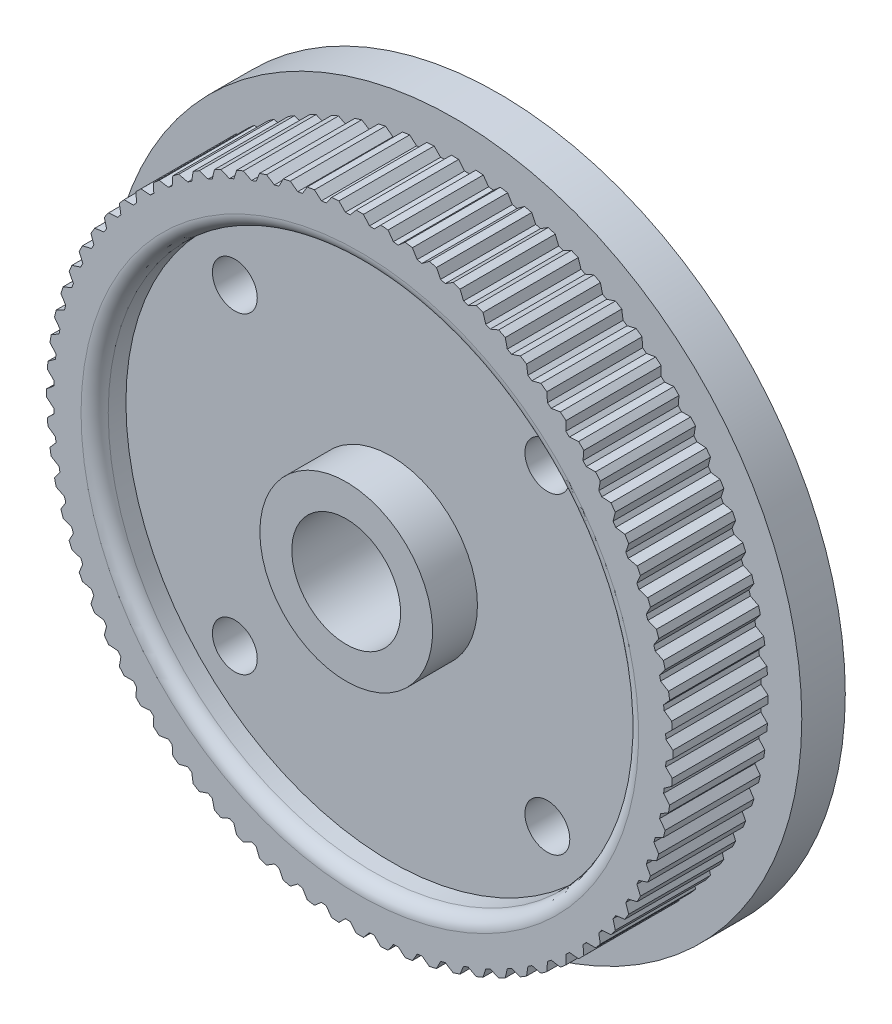
SolidWorks part; units mm, degrees
ref_plane "Front Plane" through (0, 0, 0) normal (0, 0, 1) x (1, 0, 0)
ref_plane "Top Plane" through (0, 0, 0) normal (0, 1, 0) x (1, 0, 0)
ref_plane "Right Plane" through (0, 0, 0) normal (1, 0, 0) x (0, 0, -1)
sketch "Sketch1" plane through (0, 0, 0) normal (1, 0, 0) x (0, 0, -1)
  line L0 (0, 4) -> (0, 8.5)
  line L1 (0, 8.5) -> (1, 8.5)
  line L2 (1, 8.5) -> (1, 23.025)
  line L3 (1, 23.025) -> (8, 23.025)
  line L4 (8, 25.5) -> (8, 23.025)
  line L5 (8, 25.5) -> (11.2, 25.5)
  line L6 (11.2, 25.5) -> (11.2, 8.5)
  line L7 (11.2, 8.5) -> (17.5, 8.5)
  line L8 (17.5, 8.5) -> (17.5, 4)
  line L9 (17.5, 4) -> (0, 4)
  line L10 (0, 0) -> (36.0343, 0) construction
  dimension "D1" = 8
  dimension "D2" = 17
  dimension "D3" = 17.5
  dimension "D4" = 51
  dimension "D5" = 46.05
  dimension "D6" = 8
  dimension "D7" = 1
  dimension "D8" = 11.2
revolve "Revolve1" add sketch "Sketch1" angle 360 about L10
sketch "Sketch2" plane through (0, 0, -1) normal (0, 0, 1) x (1, 0, 0)
  line L0 (0, 23.025) -> (0, 0) construction
  line L1 (0, 0) -> (1.8065, 22.954) construction
  line L2 (0.27, 23.0234) -> (0.7059, 22.5039)
  line L3 (1.0619, 22.4899) -> (1.5372, 22.9736)
  line L4 (2.8232, 22.3373) -> (3.335, 22.7822)
  line L5 (2.0756, 22.9313) -> (2.4694, 22.3792)
  line L6 (4.567, 22.0469) -> (5.1122, 22.4503)
  line L7 (3.8683, 22.6977) -> (4.2176, 22.1164)
  line L8 (6.2827, 21.6206) -> (6.8578, 21.98)
  line L9 (5.6372, 22.3242) -> (5.9398, 21.7174)
  line L10 (7.9597, 21.0611) -> (8.5612, 21.3742)
  line L11 (7.3714, 21.8131) -> (7.6254, 21.1844)
  line L12 (9.5876, 20.3716) -> (10.2118, 20.6366)
  line L13 (9.0601, 21.1675) -> (9.264, 20.5208)
  line L14 (11.1564, 19.5566) -> (11.7995, 19.7718)
  line L15 (10.693, 20.3914) -> (10.8455, 19.7307)
  line L16 (12.6564, 18.621) -> (13.3144, 18.785)
  line L17 (12.2599, 19.4896) -> (12.3602, 18.8189)
  line L18 (14.0784, 17.5706) -> (14.7472, 17.6825)
  line L19 (13.7513, 18.4676) -> (13.7986, 17.7911)
  line L20 (15.4135, 16.4118) -> (16.0891, 16.4709)
  line L21 (15.1578, 17.3318) -> (15.1519, 16.6537)
  line L22 (16.6537, 15.1519) -> (17.3318, 15.1578)
  line L23 (16.4709, 16.0891) -> (16.4118, 15.4135)
  line L24 (17.7911, 13.7986) -> (18.4676, 13.7513)
  line L25 (17.6825, 14.7472) -> (17.5706, 14.0784)
  line L26 (18.8189, 12.3602) -> (19.4896, 12.2599)
  line L27 (18.785, 13.3144) -> (18.621, 12.6564)
  line L28 (19.7307, 10.8455) -> (20.3914, 10.693)
  line L29 (19.7718, 11.7995) -> (19.5566, 11.1564)
  line L30 (20.5208, 9.264) -> (21.1675, 9.0601)
  line L31 (20.6366, 10.2118) -> (20.3716, 9.5876)
  line L32 (21.1844, 7.6254) -> (21.8131, 7.3714)
  line L33 (21.3742, 8.5612) -> (21.0611, 7.9597)
  line L34 (21.7174, 5.9398) -> (22.3242, 5.6372)
  line L35 (21.98, 6.8578) -> (21.6206, 6.2827)
  line L36 (22.1164, 4.2176) -> (22.6977, 3.8683)
  line L37 (22.4503, 5.1122) -> (22.0469, 4.567)
  line L38 (22.3792, 2.4694) -> (22.9313, 2.0756)
  line L39 (22.7822, 3.335) -> (22.3373, 2.8232)
  line L40 (22.5039, 0.7059) -> (23.0234, 0.27)
  line L41 (22.9736, 1.5372) -> (22.4899, 1.0619)
  line L42 (22.4899, -1.0619) -> (22.9736, -1.5372)
  line L43 (23.0234, -0.27) -> (22.5039, -0.7059)
  line L44 (22.3373, -2.8232) -> (22.7822, -3.335)
  line L45 (22.9313, -2.0756) -> (22.3792, -2.4694)
  line L46 (22.0469, -4.567) -> (22.4503, -5.1122)
  line L47 (22.6977, -3.8683) -> (22.1164, -4.2176)
  line L48 (21.6206, -6.2827) -> (21.98, -6.8578)
  line L49 (22.3242, -5.6372) -> (21.7174, -5.9398)
  line L50 (21.0611, -7.9597) -> (21.3742, -8.5612)
  line L51 (21.8131, -7.3714) -> (21.1844, -7.6254)
  line L52 (20.3716, -9.5876) -> (20.6366, -10.2118)
  line L53 (21.1675, -9.0601) -> (20.5208, -9.264)
  line L54 (19.5566, -11.1564) -> (19.7718, -11.7995)
  line L55 (20.3914, -10.693) -> (19.7307, -10.8455)
  line L56 (18.621, -12.6564) -> (18.785, -13.3144)
  line L57 (19.4896, -12.2599) -> (18.8189, -12.3602)
  line L58 (17.5706, -14.0784) -> (17.6825, -14.7472)
  line L59 (18.4676, -13.7513) -> (17.7911, -13.7986)
  line L60 (16.4118, -15.4135) -> (16.4709, -16.0891)
  line L61 (17.3318, -15.1578) -> (16.6537, -15.1519)
  line L62 (15.1519, -16.6537) -> (15.1578, -17.3318)
  line L63 (16.0891, -16.4709) -> (15.4135, -16.4118)
  line L64 (13.7986, -17.7911) -> (13.7513, -18.4676)
  line L65 (14.7472, -17.6825) -> (14.0784, -17.5706)
  line L66 (12.3602, -18.8189) -> (12.2599, -19.4896)
  line L67 (13.3144, -18.785) -> (12.6564, -18.621)
  line L68 (10.8455, -19.7307) -> (10.693, -20.3914)
  line L69 (11.7995, -19.7718) -> (11.1564, -19.5566)
  line L70 (9.264, -20.5208) -> (9.0601, -21.1675)
  line L71 (10.2118, -20.6366) -> (9.5876, -20.3716)
  line L72 (7.6254, -21.1844) -> (7.3714, -21.8131)
  line L73 (8.5612, -21.3742) -> (7.9597, -21.0611)
  line L74 (5.9398, -21.7174) -> (5.6372, -22.3242)
  line L75 (6.8578, -21.98) -> (6.2827, -21.6206)
  line L76 (4.2176, -22.1164) -> (3.8683, -22.6977)
  line L77 (5.1122, -22.4503) -> (4.567, -22.0469)
  line L78 (2.4694, -22.3792) -> (2.0756, -22.9313)
  line L79 (3.335, -22.7822) -> (2.8232, -22.3373)
  line L80 (0.7059, -22.5039) -> (0.27, -23.0234)
  line L81 (1.5372, -22.9736) -> (1.0619, -22.4899)
  line L82 (-1.0619, -22.4899) -> (-1.5372, -22.9736)
  line L83 (-0.27, -23.0234) -> (-0.7059, -22.5039)
  line L84 (-2.8232, -22.3373) -> (-3.335, -22.7822)
  line L85 (-2.0756, -22.9313) -> (-2.4694, -22.3792)
  line L86 (-4.567, -22.0469) -> (-5.1122, -22.4503)
  line L87 (-3.8683, -22.6977) -> (-4.2176, -22.1164)
  line L88 (-6.2827, -21.6206) -> (-6.8578, -21.98)
  line L89 (-5.6372, -22.3242) -> (-5.9398, -21.7174)
  line L90 (-7.9597, -21.0611) -> (-8.5612, -21.3742)
  line L91 (-7.3714, -21.8131) -> (-7.6254, -21.1844)
  line L92 (-9.5876, -20.3716) -> (-10.2118, -20.6366)
  line L93 (-9.0601, -21.1675) -> (-9.264, -20.5208)
  line L94 (-11.1564, -19.5566) -> (-11.7995, -19.7718)
  line L95 (-10.693, -20.3914) -> (-10.8455, -19.7307)
  line L96 (-12.6564, -18.621) -> (-13.3144, -18.785)
  line L97 (-12.2599, -19.4896) -> (-12.3602, -18.8189)
  line L98 (-14.0784, -17.5706) -> (-14.7472, -17.6825)
  line L99 (-13.7513, -18.4676) -> (-13.7986, -17.7911)
  line L100 (-15.4135, -16.4118) -> (-16.0891, -16.4709)
  line L101 (-15.1578, -17.3318) -> (-15.1519, -16.6537)
  line L102 (-16.6537, -15.1519) -> (-17.3318, -15.1578)
  line L103 (-16.4709, -16.0891) -> (-16.4118, -15.4135)
  line L104 (-17.7911, -13.7986) -> (-18.4676, -13.7513)
  line L105 (-17.6825, -14.7472) -> (-17.5706, -14.0784)
  line L106 (-18.8189, -12.3602) -> (-19.4896, -12.2599)
  line L107 (-18.785, -13.3144) -> (-18.621, -12.6564)
  line L108 (-19.7307, -10.8455) -> (-20.3914, -10.693)
  line L109 (-19.7718, -11.7995) -> (-19.5566, -11.1564)
  line L110 (-20.5208, -9.264) -> (-21.1675, -9.0601)
  line L111 (-20.6366, -10.2118) -> (-20.3716, -9.5876)
  line L112 (-21.1844, -7.6254) -> (-21.8131, -7.3714)
  line L113 (-21.3742, -8.5612) -> (-21.0611, -7.9597)
  line L114 (-21.7174, -5.9398) -> (-22.3242, -5.6372)
  line L115 (-21.98, -6.8578) -> (-21.6206, -6.2827)
  line L116 (-22.1164, -4.2176) -> (-22.6977, -3.8683)
  line L117 (-22.4503, -5.1122) -> (-22.0469, -4.567)
  line L118 (-22.3792, -2.4694) -> (-22.9313, -2.0756)
  line L119 (-22.7822, -3.335) -> (-22.3373, -2.8232)
  line L120 (-22.5039, -0.7059) -> (-23.0234, -0.27)
  line L121 (-22.9736, -1.5372) -> (-22.4899, -1.0619)
  line L122 (-22.4899, 1.0619) -> (-22.9736, 1.5372)
  line L123 (-23.0234, 0.27) -> (-22.5039, 0.7059)
  line L124 (-22.3373, 2.8232) -> (-22.7822, 3.335)
  line L125 (-22.9313, 2.0756) -> (-22.3792, 2.4694)
  line L126 (-22.0469, 4.567) -> (-22.4503, 5.1122)
  line L127 (-22.6977, 3.8683) -> (-22.1164, 4.2176)
  line L128 (-21.6206, 6.2827) -> (-21.98, 6.8578)
  line L129 (-22.3242, 5.6372) -> (-21.7174, 5.9398)
  line L130 (-21.0611, 7.9597) -> (-21.3742, 8.5612)
  line L131 (-21.8131, 7.3714) -> (-21.1844, 7.6254)
  line L132 (-20.3716, 9.5876) -> (-20.6366, 10.2118)
  line L133 (-21.1675, 9.0601) -> (-20.5208, 9.264)
  line L134 (-19.5566, 11.1564) -> (-19.7718, 11.7995)
  line L135 (-20.3914, 10.693) -> (-19.7307, 10.8455)
  line L136 (-18.621, 12.6564) -> (-18.785, 13.3144)
  line L137 (-19.4896, 12.2599) -> (-18.8189, 12.3602)
  line L138 (-17.5706, 14.0784) -> (-17.6825, 14.7472)
  line L139 (-18.4676, 13.7513) -> (-17.7911, 13.7986)
  line L140 (-16.4118, 15.4135) -> (-16.4709, 16.0891)
  line L141 (-17.3318, 15.1578) -> (-16.6537, 15.1519)
  line L142 (-15.1519, 16.6537) -> (-15.1578, 17.3318)
  line L143 (-16.0891, 16.4709) -> (-15.4135, 16.4118)
  line L144 (-13.7986, 17.7911) -> (-13.7513, 18.4676)
  line L145 (-14.7472, 17.6825) -> (-14.0784, 17.5706)
  line L146 (-12.3602, 18.8189) -> (-12.2599, 19.4896)
  line L147 (-13.3144, 18.785) -> (-12.6564, 18.621)
  line L148 (-10.8455, 19.7307) -> (-10.693, 20.3914)
  line L149 (-11.7995, 19.7718) -> (-11.1564, 19.5566)
  line L150 (-9.264, 20.5208) -> (-9.0601, 21.1675)
  line L151 (-10.2118, 20.6366) -> (-9.5876, 20.3716)
  line L152 (-7.6254, 21.1844) -> (-7.3714, 21.8131)
  line L153 (-8.5612, 21.3742) -> (-7.9597, 21.0611)
  line L154 (-5.9398, 21.7174) -> (-5.6372, 22.3242)
  line L155 (-6.8578, 21.98) -> (-6.2827, 21.6206)
  line L156 (-4.2176, 22.1164) -> (-3.8683, 22.6977)
  line L157 (-5.1122, 22.4503) -> (-4.567, 22.0469)
  line L158 (-2.4694, 22.3792) -> (-2.0756, 22.9313)
  line L159 (-3.335, 22.7822) -> (-2.8232, 22.3373)
  line L160 (-0.7059, 22.5039) -> (-0.27, 23.0234)
  line L161 (-1.5372, 22.9736) -> (-1.0619, 22.4899)
  circle A0 centre (0, 0) radius 23.025 construction
  circle A1 centre (0, 0) radius 23.025 construction
  arc A2 (0.7059, 22.5039) -> (1.0619, 22.4899) centre (0, 0) cw
  arc A3 (0.27, 23.0234) -> (0, 23.025) centre (0, 0) ccw
  arc A4 (1.5372, 22.9736) -> (1.8065, 22.954) centre (0, 0) cw
  arc A5 (3.335, 22.7822) -> (3.6019, 22.7415) centre (0, 0) cw
  arc A6 (2.4694, 22.3792) -> (2.8232, 22.3373) centre (0, 0) cw
  arc A7 (2.0756, 22.9313) -> (1.8065, 22.954) centre (0, 0) ccw
  arc A8 (5.1122, 22.4503) -> (5.3751, 22.3888) centre (0, 0) cw
  arc A9 (4.2176, 22.1164) -> (4.567, 22.0469) centre (0, 0) cw
  arc A10 (3.8683, 22.6977) -> (3.6019, 22.7415) centre (0, 0) ccw
  arc A11 (6.8578, 21.98) -> (7.1151, 21.8981) centre (0, 0) cw
  arc A12 (5.9398, 21.7174) -> (6.2827, 21.6206) centre (0, 0) cw
  arc A13 (5.6372, 22.3242) -> (5.3751, 22.3888) centre (0, 0) ccw
  arc A14 (8.5612, 21.3742) -> (8.8113, 21.2723) centre (0, 0) cw
  arc A15 (7.6254, 21.1844) -> (7.9597, 21.0611) centre (0, 0) cw
  arc A16 (7.3714, 21.8131) -> (7.1151, 21.8981) centre (0, 0) ccw
  arc A17 (10.2118, 20.6366) -> (10.4531, 20.5154) centre (0, 0) cw
  arc A18 (9.264, 20.5208) -> (9.5876, 20.3716) centre (0, 0) cw
  arc A19 (9.0601, 21.1675) -> (8.8113, 21.2723) centre (0, 0) ccw
  arc A20 (11.7995, 19.7718) -> (12.0305, 19.632) centre (0, 0) cw
  arc A21 (10.8455, 19.7307) -> (11.1564, 19.5566) centre (0, 0) cw
  arc A22 (10.693, 20.3914) -> (10.4531, 20.5154) centre (0, 0) ccw
  arc A23 (13.3144, 18.785) -> (13.5338, 18.6276) centre (0, 0) cw
  arc A24 (12.3602, 18.8189) -> (12.6564, 18.621) centre (0, 0) cw
  arc A25 (12.2599, 19.4896) -> (12.0305, 19.632) centre (0, 0) ccw
  arc A26 (14.7472, 17.6825) -> (14.9535, 17.5083) centre (0, 0) cw
  arc A27 (13.7986, 17.7911) -> (14.0784, 17.5706) centre (0, 0) cw
  arc A28 (13.7513, 18.4676) -> (13.5338, 18.6276) centre (0, 0) ccw
  arc A29 (16.0891, 16.4709) -> (16.2811, 16.2811) centre (0, 0) cw
  arc A30 (15.1519, 16.6537) -> (15.4135, 16.4118) centre (0, 0) cw
  arc A31 (15.1578, 17.3318) -> (14.9535, 17.5083) centre (0, 0) ccw
  arc A32 (17.3318, 15.1578) -> (17.5083, 14.9535) centre (0, 0) cw
  arc A33 (16.4118, 15.4135) -> (16.6537, 15.1519) centre (0, 0) cw
  arc A34 (16.4709, 16.0891) -> (16.2811, 16.2811) centre (0, 0) ccw
  arc A35 (18.4676, 13.7513) -> (18.6276, 13.5338) centre (0, 0) cw
  arc A36 (17.5706, 14.0784) -> (17.7911, 13.7986) centre (0, 0) cw
  arc A37 (17.6825, 14.7472) -> (17.5083, 14.9535) centre (0, 0) ccw
  arc A38 (19.4896, 12.2599) -> (19.632, 12.0305) centre (0, 0) cw
  arc A39 (18.621, 12.6564) -> (18.8189, 12.3602) centre (0, 0) cw
  arc A40 (18.785, 13.3144) -> (18.6276, 13.5338) centre (0, 0) ccw
  arc A41 (20.3914, 10.693) -> (20.5154, 10.4531) centre (0, 0) cw
  arc A42 (19.5566, 11.1564) -> (19.7307, 10.8455) centre (0, 0) cw
  arc A43 (19.7718, 11.7995) -> (19.632, 12.0305) centre (0, 0) ccw
  arc A44 (21.1675, 9.0601) -> (21.2723, 8.8113) centre (0, 0) cw
  arc A45 (20.3716, 9.5876) -> (20.5208, 9.264) centre (0, 0) cw
  arc A46 (20.6366, 10.2118) -> (20.5154, 10.4531) centre (0, 0) ccw
  arc A47 (21.8131, 7.3714) -> (21.8981, 7.1151) centre (0, 0) cw
  arc A48 (21.0611, 7.9597) -> (21.1844, 7.6254) centre (0, 0) cw
  arc A49 (21.3742, 8.5612) -> (21.2723, 8.8113) centre (0, 0) ccw
  arc A50 (22.3242, 5.6372) -> (22.3888, 5.3751) centre (0, 0) cw
  arc A51 (21.6206, 6.2827) -> (21.7174, 5.9398) centre (0, 0) cw
  arc A52 (21.98, 6.8578) -> (21.8981, 7.1151) centre (0, 0) ccw
  arc A53 (22.6977, 3.8683) -> (22.7415, 3.6019) centre (0, 0) cw
  arc A54 (22.0469, 4.567) -> (22.1164, 4.2176) centre (0, 0) cw
  arc A55 (22.4503, 5.1122) -> (22.3888, 5.3751) centre (0, 0) ccw
  arc A56 (22.9313, 2.0756) -> (22.954, 1.8065) centre (0, 0) cw
  arc A57 (22.3373, 2.8232) -> (22.3792, 2.4694) centre (0, 0) cw
  arc A58 (22.7822, 3.335) -> (22.7415, 3.6019) centre (0, 0) ccw
  arc A59 (23.0234, 0.27) -> (23.025, 0) centre (0, 0) cw
  arc A60 (22.4899, 1.0619) -> (22.5039, 0.7059) centre (0, 0) cw
  arc A61 (22.9736, 1.5372) -> (22.954, 1.8065) centre (0, 0) ccw
  arc A62 (22.9736, -1.5372) -> (22.954, -1.8065) centre (0, 0) cw
  arc A63 (22.5039, -0.7059) -> (22.4899, -1.0619) centre (0, 0) cw
  arc A64 (23.0234, -0.27) -> (23.025, 0) centre (0, 0) ccw
  arc A65 (22.7822, -3.335) -> (22.7415, -3.6019) centre (0, 0) cw
  arc A66 (22.3792, -2.4694) -> (22.3373, -2.8232) centre (0, 0) cw
  arc A67 (22.9313, -2.0756) -> (22.954, -1.8065) centre (0, 0) ccw
  arc A68 (22.4503, -5.1122) -> (22.3888, -5.3751) centre (0, 0) cw
  arc A69 (22.1164, -4.2176) -> (22.0469, -4.567) centre (0, 0) cw
  arc A70 (22.6977, -3.8683) -> (22.7415, -3.6019) centre (0, 0) ccw
  arc A71 (21.98, -6.8578) -> (21.8981, -7.1151) centre (0, 0) cw
  arc A72 (21.7174, -5.9398) -> (21.6206, -6.2827) centre (0, 0) cw
  arc A73 (22.3242, -5.6372) -> (22.3888, -5.3751) centre (0, 0) ccw
  arc A74 (21.3742, -8.5612) -> (21.2723, -8.8113) centre (0, 0) cw
  arc A75 (21.1844, -7.6254) -> (21.0611, -7.9597) centre (0, 0) cw
  arc A76 (21.8131, -7.3714) -> (21.8981, -7.1151) centre (0, 0) ccw
  arc A77 (20.6366, -10.2118) -> (20.5154, -10.4531) centre (0, 0) cw
  arc A78 (20.5208, -9.264) -> (20.3716, -9.5876) centre (0, 0) cw
  arc A79 (21.1675, -9.0601) -> (21.2723, -8.8113) centre (0, 0) ccw
  arc A80 (19.7718, -11.7995) -> (19.632, -12.0305) centre (0, 0) cw
  arc A81 (19.7307, -10.8455) -> (19.5566, -11.1564) centre (0, 0) cw
  arc A82 (20.3914, -10.693) -> (20.5154, -10.4531) centre (0, 0) ccw
  arc A83 (18.785, -13.3144) -> (18.6276, -13.5338) centre (0, 0) cw
  arc A84 (18.8189, -12.3602) -> (18.621, -12.6564) centre (0, 0) cw
  arc A85 (19.4896, -12.2599) -> (19.632, -12.0305) centre (0, 0) ccw
  arc A86 (17.6825, -14.7472) -> (17.5083, -14.9535) centre (0, 0) cw
  arc A87 (17.7911, -13.7986) -> (17.5706, -14.0784) centre (0, 0) cw
  arc A88 (18.4676, -13.7513) -> (18.6276, -13.5338) centre (0, 0) ccw
  arc A89 (16.4709, -16.0891) -> (16.2811, -16.2811) centre (0, 0) cw
  arc A90 (16.6537, -15.1519) -> (16.4118, -15.4135) centre (0, 0) cw
  arc A91 (17.3318, -15.1578) -> (17.5083, -14.9535) centre (0, 0) ccw
  arc A92 (15.1578, -17.3318) -> (14.9535, -17.5083) centre (0, 0) cw
  arc A93 (15.4135, -16.4118) -> (15.1519, -16.6537) centre (0, 0) cw
  arc A94 (16.0891, -16.4709) -> (16.2811, -16.2811) centre (0, 0) ccw
  arc A95 (13.7513, -18.4676) -> (13.5338, -18.6276) centre (0, 0) cw
  arc A96 (14.0784, -17.5706) -> (13.7986, -17.7911) centre (0, 0) cw
  arc A97 (14.7472, -17.6825) -> (14.9535, -17.5083) centre (0, 0) ccw
  arc A98 (12.2599, -19.4896) -> (12.0305, -19.632) centre (0, 0) cw
  arc A99 (12.6564, -18.621) -> (12.3602, -18.8189) centre (0, 0) cw
  arc A100 (13.3144, -18.785) -> (13.5338, -18.6276) centre (0, 0) ccw
  arc A101 (10.693, -20.3914) -> (10.4531, -20.5154) centre (0, 0) cw
  arc A102 (11.1564, -19.5566) -> (10.8455, -19.7307) centre (0, 0) cw
  arc A103 (11.7995, -19.7718) -> (12.0305, -19.632) centre (0, 0) ccw
  arc A104 (9.0601, -21.1675) -> (8.8113, -21.2723) centre (0, 0) cw
  arc A105 (9.5876, -20.3716) -> (9.264, -20.5208) centre (0, 0) cw
  arc A106 (10.2118, -20.6366) -> (10.4531, -20.5154) centre (0, 0) ccw
  arc A107 (7.3714, -21.8131) -> (7.1151, -21.8981) centre (0, 0) cw
  arc A108 (7.9597, -21.0611) -> (7.6254, -21.1844) centre (0, 0) cw
  arc A109 (8.5612, -21.3742) -> (8.8113, -21.2723) centre (0, 0) ccw
  arc A110 (5.6372, -22.3242) -> (5.3751, -22.3888) centre (0, 0) cw
  arc A111 (6.2827, -21.6206) -> (5.9398, -21.7174) centre (0, 0) cw
  arc A112 (6.8578, -21.98) -> (7.1151, -21.8981) centre (0, 0) ccw
  arc A113 (3.8683, -22.6977) -> (3.6019, -22.7415) centre (0, 0) cw
  arc A114 (4.567, -22.0469) -> (4.2176, -22.1164) centre (0, 0) cw
  arc A115 (5.1122, -22.4503) -> (5.3751, -22.3888) centre (0, 0) ccw
  arc A116 (2.0756, -22.9313) -> (1.8065, -22.954) centre (0, 0) cw
  arc A117 (2.8232, -22.3373) -> (2.4694, -22.3792) centre (0, 0) cw
  arc A118 (3.335, -22.7822) -> (3.6019, -22.7415) centre (0, 0) ccw
  arc A119 (0.27, -23.0234) -> (0, -23.025) centre (0, 0) cw
  arc A120 (1.0619, -22.4899) -> (0.7059, -22.5039) centre (0, 0) cw
  arc A121 (1.5372, -22.9736) -> (1.8065, -22.954) centre (0, 0) ccw
  arc A122 (-1.5372, -22.9736) -> (-1.8065, -22.954) centre (0, 0) cw
  arc A123 (-0.7059, -22.5039) -> (-1.0619, -22.4899) centre (0, 0) cw
  arc A124 (-0.27, -23.0234) -> (0, -23.025) centre (0, 0) ccw
  arc A125 (-3.335, -22.7822) -> (-3.6019, -22.7415) centre (0, 0) cw
  arc A126 (-2.4694, -22.3792) -> (-2.8232, -22.3373) centre (0, 0) cw
  arc A127 (-2.0756, -22.9313) -> (-1.8065, -22.954) centre (0, 0) ccw
  arc A128 (-5.1122, -22.4503) -> (-5.3751, -22.3888) centre (0, 0) cw
  arc A129 (-4.2176, -22.1164) -> (-4.567, -22.0469) centre (0, 0) cw
  arc A130 (-3.8683, -22.6977) -> (-3.6019, -22.7415) centre (0, 0) ccw
  arc A131 (-6.8578, -21.98) -> (-7.1151, -21.8981) centre (0, 0) cw
  arc A132 (-5.9398, -21.7174) -> (-6.2827, -21.6206) centre (0, 0) cw
  arc A133 (-5.6372, -22.3242) -> (-5.3751, -22.3888) centre (0, 0) ccw
  arc A134 (-8.5612, -21.3742) -> (-8.8113, -21.2723) centre (0, 0) cw
  arc A135 (-7.6254, -21.1844) -> (-7.9597, -21.0611) centre (0, 0) cw
  arc A136 (-7.3714, -21.8131) -> (-7.1151, -21.8981) centre (0, 0) ccw
  arc A137 (-10.2118, -20.6366) -> (-10.4531, -20.5154) centre (0, 0) cw
  arc A138 (-9.264, -20.5208) -> (-9.5876, -20.3716) centre (0, 0) cw
  arc A139 (-9.0601, -21.1675) -> (-8.8113, -21.2723) centre (0, 0) ccw
  arc A140 (-11.7995, -19.7718) -> (-12.0305, -19.632) centre (0, 0) cw
  arc A141 (-10.8455, -19.7307) -> (-11.1564, -19.5566) centre (0, 0) cw
  arc A142 (-10.693, -20.3914) -> (-10.4531, -20.5154) centre (0, 0) ccw
  arc A143 (-13.3144, -18.785) -> (-13.5338, -18.6276) centre (0, 0) cw
  arc A144 (-12.3602, -18.8189) -> (-12.6564, -18.621) centre (0, 0) cw
  arc A145 (-12.2599, -19.4896) -> (-12.0305, -19.632) centre (0, 0) ccw
  arc A146 (-14.7472, -17.6825) -> (-14.9535, -17.5083) centre (0, 0) cw
  arc A147 (-13.7986, -17.7911) -> (-14.0784, -17.5706) centre (0, 0) cw
  arc A148 (-13.7513, -18.4676) -> (-13.5338, -18.6276) centre (0, 0) ccw
  arc A149 (-16.0891, -16.4709) -> (-16.2811, -16.2811) centre (0, 0) cw
  arc A150 (-15.1519, -16.6537) -> (-15.4135, -16.4118) centre (0, 0) cw
  arc A151 (-15.1578, -17.3318) -> (-14.9535, -17.5083) centre (0, 0) ccw
  arc A152 (-17.3318, -15.1578) -> (-17.5083, -14.9535) centre (0, 0) cw
  arc A153 (-16.4118, -15.4135) -> (-16.6537, -15.1519) centre (0, 0) cw
  arc A154 (-16.4709, -16.0891) -> (-16.2811, -16.2811) centre (0, 0) ccw
  arc A155 (-18.4676, -13.7513) -> (-18.6276, -13.5338) centre (0, 0) cw
  arc A156 (-17.5706, -14.0784) -> (-17.7911, -13.7986) centre (0, 0) cw
  arc A157 (-17.6825, -14.7472) -> (-17.5083, -14.9535) centre (0, 0) ccw
  arc A158 (-19.4896, -12.2599) -> (-19.632, -12.0305) centre (0, 0) cw
  arc A159 (-18.621, -12.6564) -> (-18.8189, -12.3602) centre (0, 0) cw
  arc A160 (-18.785, -13.3144) -> (-18.6276, -13.5338) centre (0, 0) ccw
  arc A161 (-20.3914, -10.693) -> (-20.5154, -10.4531) centre (0, 0) cw
  arc A162 (-19.5566, -11.1564) -> (-19.7307, -10.8455) centre (0, 0) cw
  arc A163 (-19.7718, -11.7995) -> (-19.632, -12.0305) centre (0, 0) ccw
  arc A164 (-21.1675, -9.0601) -> (-21.2723, -8.8113) centre (0, 0) cw
  arc A165 (-20.3716, -9.5876) -> (-20.5208, -9.264) centre (0, 0) cw
  arc A166 (-20.6366, -10.2118) -> (-20.5154, -10.4531) centre (0, 0) ccw
  arc A167 (-21.8131, -7.3714) -> (-21.8981, -7.1151) centre (0, 0) cw
  arc A168 (-21.0611, -7.9597) -> (-21.1844, -7.6254) centre (0, 0) cw
  arc A169 (-21.3742, -8.5612) -> (-21.2723, -8.8113) centre (0, 0) ccw
  arc A170 (-22.3242, -5.6372) -> (-22.3888, -5.3751) centre (0, 0) cw
  arc A171 (-21.6206, -6.2827) -> (-21.7174, -5.9398) centre (0, 0) cw
  arc A172 (-21.98, -6.8578) -> (-21.8981, -7.1151) centre (0, 0) ccw
  arc A173 (-22.6977, -3.8683) -> (-22.7415, -3.6019) centre (0, 0) cw
  arc A174 (-22.0469, -4.567) -> (-22.1164, -4.2176) centre (0, 0) cw
  arc A175 (-22.4503, -5.1122) -> (-22.3888, -5.3751) centre (0, 0) ccw
  arc A176 (-22.9313, -2.0756) -> (-22.954, -1.8065) centre (0, 0) cw
  arc A177 (-22.3373, -2.8232) -> (-22.3792, -2.4694) centre (0, 0) cw
  arc A178 (-22.7822, -3.335) -> (-22.7415, -3.6019) centre (0, 0) ccw
  arc A179 (-23.0234, -0.27) -> (-23.025, 0) centre (0, 0) cw
  arc A180 (-22.4899, -1.0619) -> (-22.5039, -0.7059) centre (0, 0) cw
  arc A181 (-22.9736, -1.5372) -> (-22.954, -1.8065) centre (0, 0) ccw
  arc A182 (-22.9736, 1.5372) -> (-22.954, 1.8065) centre (0, 0) cw
  arc A183 (-22.5039, 0.7059) -> (-22.4899, 1.0619) centre (0, 0) cw
  arc A184 (-23.0234, 0.27) -> (-23.025, 0) centre (0, 0) ccw
  arc A185 (-22.7822, 3.335) -> (-22.7415, 3.6019) centre (0, 0) cw
  arc A186 (-22.3792, 2.4694) -> (-22.3373, 2.8232) centre (0, 0) cw
  arc A187 (-22.9313, 2.0756) -> (-22.954, 1.8065) centre (0, 0) ccw
  arc A188 (-22.4503, 5.1122) -> (-22.3888, 5.3751) centre (0, 0) cw
  arc A189 (-22.1164, 4.2176) -> (-22.0469, 4.567) centre (0, 0) cw
  arc A190 (-22.6977, 3.8683) -> (-22.7415, 3.6019) centre (0, 0) ccw
  arc A191 (-21.98, 6.8578) -> (-21.8981, 7.1151) centre (0, 0) cw
  arc A192 (-21.7174, 5.9398) -> (-21.6206, 6.2827) centre (0, 0) cw
  arc A193 (-22.3242, 5.6372) -> (-22.3888, 5.3751) centre (0, 0) ccw
  arc A194 (-21.3742, 8.5612) -> (-21.2723, 8.8113) centre (0, 0) cw
  arc A195 (-21.1844, 7.6254) -> (-21.0611, 7.9597) centre (0, 0) cw
  arc A196 (-21.8131, 7.3714) -> (-21.8981, 7.1151) centre (0, 0) ccw
  arc A197 (-20.6366, 10.2118) -> (-20.5154, 10.4531) centre (0, 0) cw
  arc A198 (-20.5208, 9.264) -> (-20.3716, 9.5876) centre (0, 0) cw
  arc A199 (-21.1675, 9.0601) -> (-21.2723, 8.8113) centre (0, 0) ccw
  arc A200 (-19.7718, 11.7995) -> (-19.632, 12.0305) centre (0, 0) cw
  arc A201 (-19.7307, 10.8455) -> (-19.5566, 11.1564) centre (0, 0) cw
  arc A202 (-20.3914, 10.693) -> (-20.5154, 10.4531) centre (0, 0) ccw
  arc A203 (-18.785, 13.3144) -> (-18.6276, 13.5338) centre (0, 0) cw
  arc A204 (-18.8189, 12.3602) -> (-18.621, 12.6564) centre (0, 0) cw
  arc A205 (-19.4896, 12.2599) -> (-19.632, 12.0305) centre (0, 0) ccw
  arc A206 (-17.6825, 14.7472) -> (-17.5083, 14.9535) centre (0, 0) cw
  arc A207 (-17.7911, 13.7986) -> (-17.5706, 14.0784) centre (0, 0) cw
  arc A208 (-18.4676, 13.7513) -> (-18.6276, 13.5338) centre (0, 0) ccw
  arc A209 (-16.4709, 16.0891) -> (-16.2811, 16.2811) centre (0, 0) cw
  arc A210 (-16.6537, 15.1519) -> (-16.4118, 15.4135) centre (0, 0) cw
  arc A211 (-17.3318, 15.1578) -> (-17.5083, 14.9535) centre (0, 0) ccw
  arc A212 (-15.1578, 17.3318) -> (-14.9535, 17.5083) centre (0, 0) cw
  arc A213 (-15.4135, 16.4118) -> (-15.1519, 16.6537) centre (0, 0) cw
  arc A214 (-16.0891, 16.4709) -> (-16.2811, 16.2811) centre (0, 0) ccw
  arc A215 (-13.7513, 18.4676) -> (-13.5338, 18.6276) centre (0, 0) cw
  arc A216 (-14.0784, 17.5706) -> (-13.7986, 17.7911) centre (0, 0) cw
  arc A217 (-14.7472, 17.6825) -> (-14.9535, 17.5083) centre (0, 0) ccw
  arc A218 (-12.2599, 19.4896) -> (-12.0305, 19.632) centre (0, 0) cw
  arc A219 (-12.6564, 18.621) -> (-12.3602, 18.8189) centre (0, 0) cw
  arc A220 (-13.3144, 18.785) -> (-13.5338, 18.6276) centre (0, 0) ccw
  arc A221 (-10.693, 20.3914) -> (-10.4531, 20.5154) centre (0, 0) cw
  arc A222 (-11.1564, 19.5566) -> (-10.8455, 19.7307) centre (0, 0) cw
  arc A223 (-11.7995, 19.7718) -> (-12.0305, 19.632) centre (0, 0) ccw
  arc A224 (-9.0601, 21.1675) -> (-8.8113, 21.2723) centre (0, 0) cw
  arc A225 (-9.5876, 20.3716) -> (-9.264, 20.5208) centre (0, 0) cw
  arc A226 (-10.2118, 20.6366) -> (-10.4531, 20.5154) centre (0, 0) ccw
  arc A227 (-7.3714, 21.8131) -> (-7.1151, 21.8981) centre (0, 0) cw
  arc A228 (-7.9597, 21.0611) -> (-7.6254, 21.1844) centre (0, 0) cw
  arc A229 (-8.5612, 21.3742) -> (-8.8113, 21.2723) centre (0, 0) ccw
  arc A230 (-5.6372, 22.3242) -> (-5.3751, 22.3888) centre (0, 0) cw
  arc A231 (-6.2827, 21.6206) -> (-5.9398, 21.7174) centre (0, 0) cw
  arc A232 (-6.8578, 21.98) -> (-7.1151, 21.8981) centre (0, 0) ccw
  arc A233 (-3.8683, 22.6977) -> (-3.6019, 22.7415) centre (0, 0) cw
  arc A234 (-4.567, 22.0469) -> (-4.2176, 22.1164) centre (0, 0) cw
  arc A235 (-5.1122, 22.4503) -> (-5.3751, 22.3888) centre (0, 0) ccw
  arc A236 (-2.0756, 22.9313) -> (-1.8065, 22.954) centre (0, 0) cw
  arc A237 (-2.8232, 22.3373) -> (-2.4694, 22.3792) centre (0, 0) cw
  arc A238 (-3.335, 22.7822) -> (-3.6019, 22.7415) centre (0, 0) ccw
  arc A239 (-0.27, 23.0234) -> (0, 23.025) centre (0, 0) cw
  arc A240 (-1.0619, 22.4899) -> (-0.7059, 22.5039) centre (0, 0) cw
  arc A241 (-1.5372, 22.9736) -> (-1.8065, 22.954) centre (0, 0) ccw
  circle A242 centre (0, 0) radius 26.9339
  point P491 (0, 0)
  dimension "D3" = 0.51
  dimension "D1" = 40
  dimension "D2" = 40
  dimension "D5" = 0.54
  dimension "D4" = 80
extrude "Cut-Extrude1" cut sketch "Sketch2" against normal up to surface (7 mm away) up to face at (23.025, 0, -8)
sketch "Sketch3" plane through (0, 0, 0) normal (0, 1, 0) x (1, 0, 0)
  line L0 (8.5, 17.5) -> (-8.5, 17.5) construction
  circle A0 centre (0, 14.5) radius 1.5
  dimension "D1" = 3
  dimension "D2" = 3
extrude "Cut-Extrude2" [suppressed] cut sketch "Sketch3" against normal through all both and the other way through all
sketch "Sketch4" plane through (0, 0, -1) normal (0, 0, 1) x (1, 0, 0)
  circle A0 centre (0, 0) radius 19.5
  circle A1 centre (0, 0) radius 6.35
  dimension "D1" = 39
  dimension "D2" = 12.7
extrude "Cut-Extrude3" cut sketch "Sketch4" against normal blind 2.3 and the other way blind 10
fillet "Fillet1" radius 1 1 edges at (-19.5, 0, -1)
sketch "Sketch5" plane through (0, 0, -11.2) normal (0, 0, -1) x (-1, 0, 0)
  circle A0 centre (0, 0) radius 19.5
  circle A1 centre (0, 0) radius 8.5
  circle A2 centre (0, 0) radius 8.5 construction
  dimension "D1" = 39
extrude "Cut-Extrude4" cut sketch "Sketch5" against normal blind 4
sketch "Sketch6" plane through (0, 0, -7.2) normal (0, 0, -1) x (-1, 0, 0)
  line L0 (0, 0) -> (0, 16.25) construction
  line L2 (-11.4905, 11.4905) -> (0, 0) construction
  circle A0 centre (-11.4905, 11.4905) radius 1.65
  circle A1 centre (11.4905, 11.4905) radius 1.65
  circle A2 centre (11.4905, -11.4905) radius 1.65
  circle A3 centre (-11.4905, -11.4905) radius 1.65
  circle A4 centre (0, 0) radius 16.25 construction
  point P12 (0, 0)
  dimension "D2" = 3.3
  dimension "D3" = 32.5
  dimension "D4" = 45
  dimension "D1" = 4
extrude "Cut-Extrude5" cut sketch "Sketch6" against normal through all
equation "\"c\"= .3"
equation "\"c2\"= .25"
